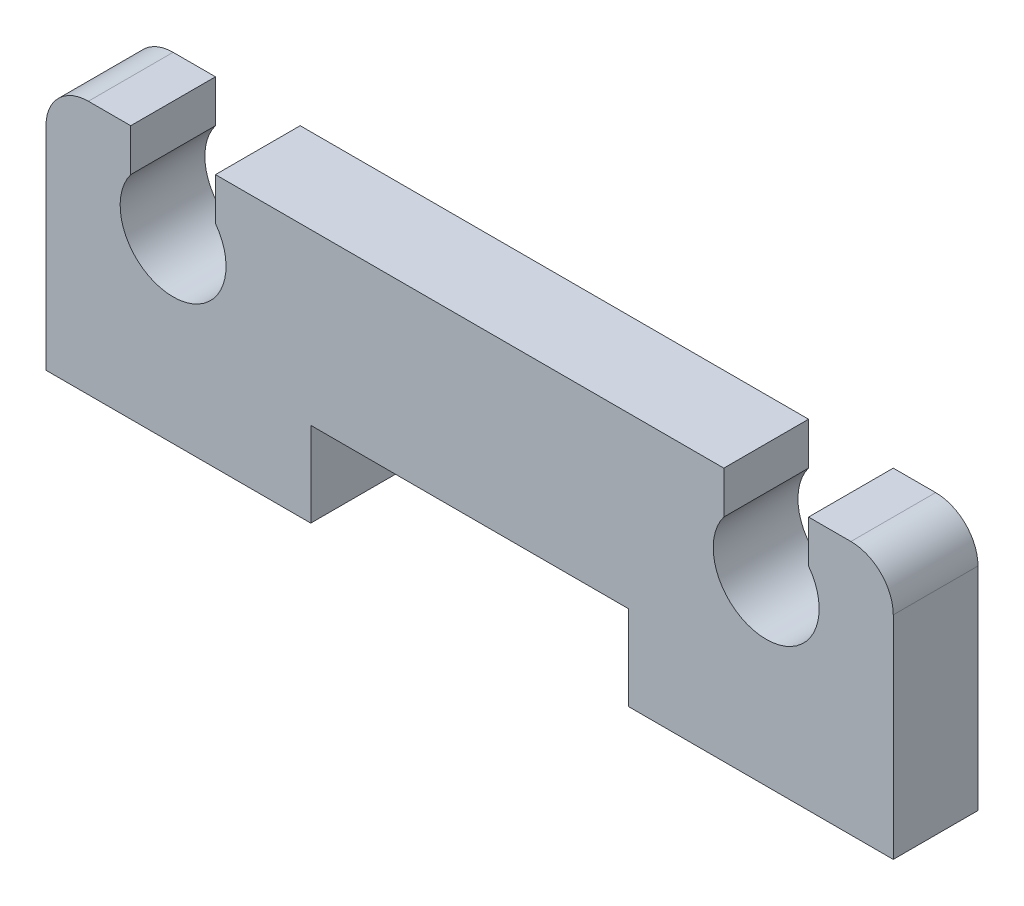
SolidWorks part; units mm, degrees
material "Acrylic (Medium-high impact)"
ref_plane "Front Plane" through (0, 0, 0) normal (0, 0, 1) x (1, 0, 0)
ref_plane "Top Plane" through (0, 0, 0) normal (0, 1, 0) x (1, 0, 0)
ref_plane "Right Plane" through (0, 0, 0) normal (1, 0, 0) x (0, 0, -1)
sketch "Model" plane through (0, 0, 0) normal (0, 0, 1) x (1, 0, 0)
  line L12 (6.25, 2) -> (13.75, 2)
  line L54 (2, 6) -> (2, 5)
  line L55 (4, 6) -> (4, 5)
  line L56 (18, 6) -> (18, 5)
  line L57 (16, 6) -> (16, 5)
  line L58 (18, 6) -> (19, 6)
  line L59 (2, 6) -> (1, 6)
  line L104 (0, 0) -> (6.25, 0)
  line L105 (13.75, 0) -> (20, 0)
  line L106 (4, 6) -> (16, 6)
  line L185 (13.75, 2) -> (13.75, 0)
  line L186 (20, 5) -> (20, 0)
  line L187 (6.25, 2) -> (6.25, 0)
  line L188 (0, 0) -> (0, 5)
  arc A16 (1, 6) -> (0, 5) centre (1, 5) ccw
  arc A17 (20, 5) -> (19, 6) centre (19, 5) ccw
  arc A18 (2, 5) -> (4, 5) centre (3, 4.25) ccw
  arc A37 (16, 5) -> (18, 5) centre (17, 4.25) ccw
  dimension "D1" = 1
  dimension "D2" = 1.25
  dimension "D3" = 3
  dimension "D4" = 6.25
  dimension "D5" = 13.75
  dimension "D6" = 2
  dimension "D7" = 4.25
extrude "Boss-Extrude1" add sketch "Model" along normal blind 2
